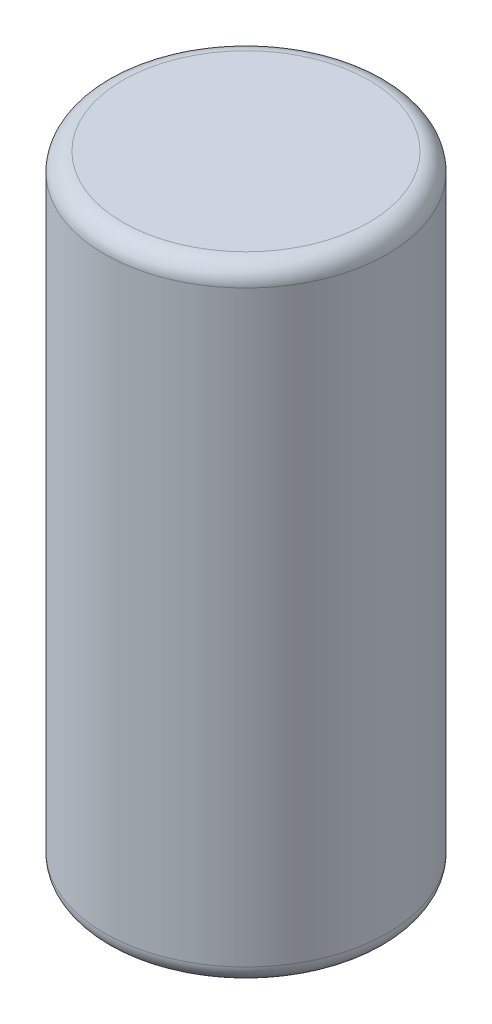
SolidWorks part; units mm, degrees
material "Ti-6Al-4VSolution treated and aged (SS)"
ref_plane "Front Plane" through (0, 0, 0) normal (0, 0, 1) x (1, 0, 0)
ref_plane "Top Plane" through (0, 0, 0) normal (0, 1, 0) x (1, 0, 0)
ref_plane "Right Plane" through (0, 0, 0) normal (1, 0, 0) x (0, 0, -1)
sketch "Sketch1" plane through (0, 0, 0) normal (0, 1, 0) x (1, 0, 0)
  circle A0 centre (0, 0) radius 77
  dimension "D1" = 154
extrude "Boss-Extrude1" add sketch "Sketch1" along normal blind 340
fillet "Fillet1" radius 10 2 edges at (0, 340, 77) (0, 0, 77)
